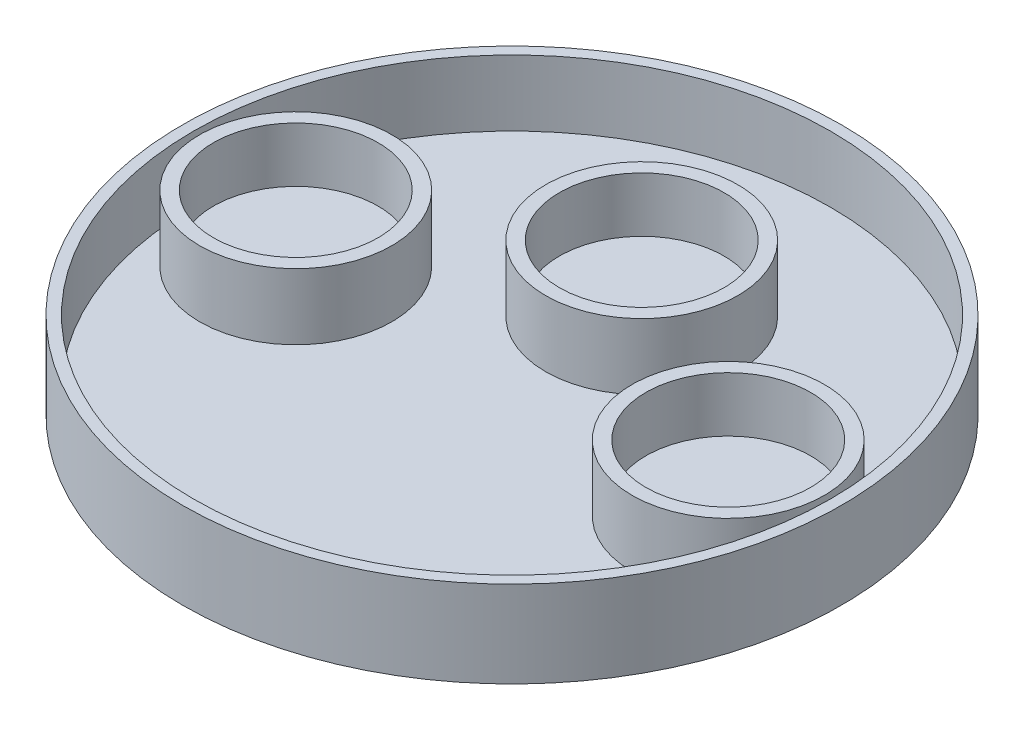
SolidWorks part; units mm, degrees
ref_plane "Front Plane" through (0, 0, 0) normal (0, 0, 1) x (1, 0, 0)
ref_plane "Top Plane" through (0, 0, 0) normal (0, 1, 0) x (1, 0, 0)
ref_plane "Right Plane" through (0, 0, 0) normal (1, 0, 0) x (0, 0, -1)
sketch "Sketch1" plane through (0, 0, 0) normal (0, 1, 0) x (1, 0, 0)
  circle A0 centre (0, 0) radius 38.1
  dimension "D1" = 76.2
extrude "Boss-Extrude1" add sketch "Sketch1" along normal blind 10
sketch "Sketch2" plane through (0, 10, 0) normal (0, 1, 0) x (1, 0, 0)
  circle A0 centre (25, 0) radius 9.525
  circle A1 centre (-25, 0) radius 9.525
  circle A2 centre (0, 15) radius 9.525
  dimension "D1" = 19.05
  dimension "D3" = 19.05
  dimension "D4" = 25
  dimension "D5" = 19.05
  dimension "D2" = 25
  dimension "D6" = 15
extrude "Cut-Extrude1" cut sketch "Sketch2" against normal blind 6.35
sketch "Sketch3" plane through (0, 10, 0) normal (0, 1, 0) x (1, 0, 0)
  circle A0 centre (0, 15) radius 11.1125
  circle A1 centre (25, 0) radius 11.115
  circle A2 centre (-25, 0) radius 11.115
  circle A3 centre (0, 0) radius 36.83
  dimension "D1" = 73.66
  dimension "D2" = 22.225
  dimension "D3" = 22.23
  dimension "D4" = 22.23
extrude "Cut-Extrude2" cut sketch "Sketch3" against normal blind 7.62
